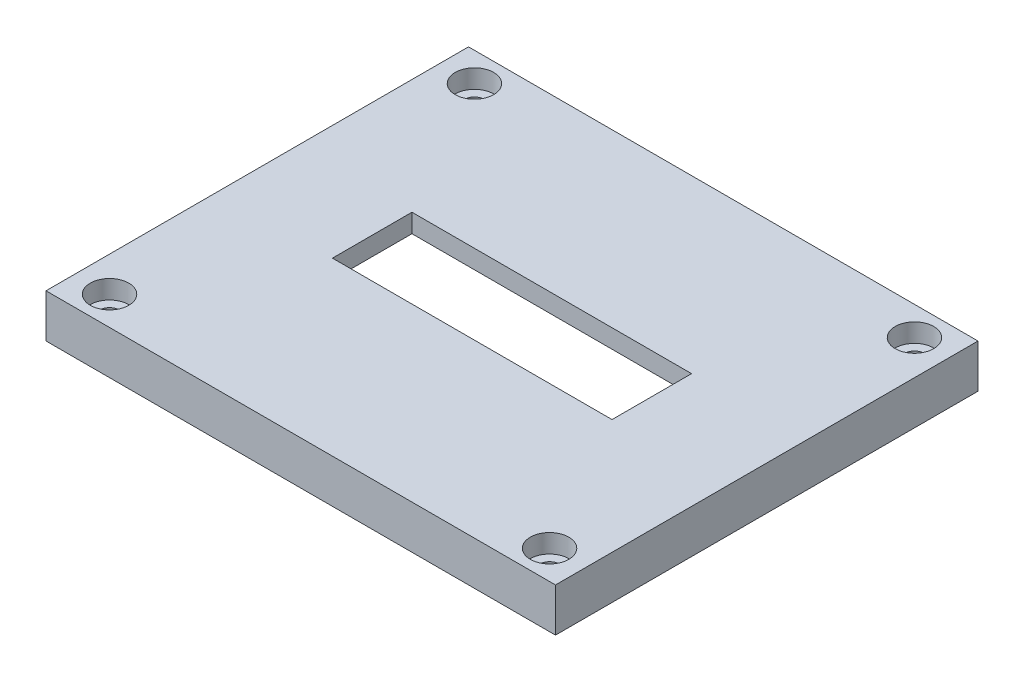
SolidWorks part; units mm, degrees
ref_plane "Спереди" through (0, 0, 0) normal (0, 0, 1) x (1, 0, 0)
ref_plane "Сверху" through (0, 0, 0) normal (0, 1, 0) x (1, 0, 0)
ref_plane "Справа" through (0, 0, 0) normal (1, 0, 0) x (0, 0, -1)
sketch "Sketch1" plane through (0, 0, 0) normal (0, 1, 0) x (1, 0, 0)
  line L1 (38, -31) -> (-38, -31)
  line L2 (38, -31) -> (38, 31)
  line L3 (38, 31) -> (-38, 31)
  line L4 (-38, -31) -> (-38, 31)
  line L5 (38, -31) -> (-38, 31) construction
  line L6 (38, 31) -> (-38, -31) construction
  point P0 (0, 0)
  dimension "D1" = 76
  dimension "D2" = 62
extrude "Boss-Extrude1" add sketch "Sketch1" along normal blind 2
sketch "Sketch2" plane through (0, 2, 0) normal (0, 1, 0) x (1, 0, 0)
  line L1 (-41, 34) -> (41, 34)
  line L2 (-41, 34) -> (-41, -34)
  line L3 (-41, -34) -> (41, -34)
  line L4 (41, 34) -> (41, -34)
  line L5 (-41, 34) -> (41, -34) construction
  line L6 (-41, -34) -> (41, 34) construction
  point P0 (0, 0)
  dimension "D1" = 82
  dimension "D2" = 68
extrude "Boss-Extrude2" add sketch "Sketch2" along normal blind 8
sketch "Sketch3" plane through (0, 0, 0) normal (0, -1, 0) x (1, 0, 0)
  line L0 (38, 0) -> (-38, 0) construction
  line L3 (38, 31) -> (38, -31) construction
  line L4 (-38, -31) -> (-38, 31) construction
  line L9 (-22.5, 6.4) -> (22.5, 6.4)
  line L10 (-22.5, 6.4) -> (-22.5, -6.4)
  line L11 (-22.5, -6.4) -> (22.5, -6.4)
  line L12 (22.5, 6.4) -> (22.5, -6.4)
  line L13 (-22.5, 6.4) -> (22.5, -6.4) construction
  line L14 (-22.5, -6.4) -> (22.5, 6.4) construction
  point P6 (0, 0)
  dimension "D1" = 45
  dimension "D2" = 12.8
extrude "Cut-Extrude1" cut sketch "Sketch3" against normal through all
sketch "Sketch4" plane through (0, 10, 0) normal (0, 1, 0) x (1, 0, 0)
  line L0 (41, 34) -> (-41, -34) construction
  line L1 (-41, 34) -> (41, -34) construction
  line L2 (-35.4089, 29.3635) -> (35.4089, 29.3635) construction
  line L3 (35.4089, 29.3635) -> (35.4089, -29.3635) construction
  line L4 (35.4089, -29.3635) -> (-35.4089, -29.3635) construction
  line L5 (-35.4089, -29.3635) -> (-35.4089, 29.3635) construction
  line L7 (-35.4089, -29.3635) -> (35.4089, 29.3635) construction
  line L8 (-35.4089, 29.3635) -> (35.4089, -29.3635) construction
  circle A0 centre (-35.4089, 29.3635) radius 1.6
  circle A1 centre (35.4089, 29.3635) radius 1.6
  circle A2 centre (35.4089, -29.3635) radius 1.6
  circle A3 centre (-35.4089, -29.3635) radius 1.6
  point P8 (0, 0)
  dimension "D2" = 3.2
  dimension "D1" = 92
extrude "Cut-Extrude2" cut sketch "Sketch4" against normal through all
sketch "Sketch5" plane through (0, 10, 0) normal (0, 1, 0) x (1, 0, 0)
  circle A0 centre (-35.4089, 29.3635) radius 3.1
  circle A1 centre (35.4089, 29.3635) radius 3.1
  circle A2 centre (35.4089, -29.3635) radius 3.1
  circle A3 centre (-35.4089, -29.3635) radius 3.1
  dimension "D1" = 6.2
extrude "Cut-Extrude3" cut sketch "Sketch5" against normal blind 3
sketch "Sketch9" plane through (0, 0, 0) normal (0, -1, 0) x (1, 0, 0)
  line L0 (-38, 31) -> (38, 31) construction
  line L1 (37.8, -30.8) -> (-37.8, -30.8)
  line L2 (37.8, -30.8) -> (37.8, 30.8)
  line L3 (37.8, 30.8) -> (-37.8, 30.8)
  line L4 (-37.8, -30.8) -> (-37.8, 30.8)
  line L5 (37.8, -30.8) -> (-37.8, 30.8) construction
  line L6 (37.8, 30.8) -> (-37.8, -30.8) construction
  line L7 (-38, -31) -> (-38, 31) construction
  point P0 (0, 0)
  dimension "D1" = 0.2
  dimension "D2" = 0.2
extrude "Cut-Extrude5" cut sketch "Sketch9" against normal blind 3 flip side to cut
sketch "Sketch10" plane through (0, 0, 0) normal (0, -1, 0) x (1, 0, 0)
  line L0 (-37.8, -30.8) -> (-31.8, -30.8)
  line L1 (-37.8, 24.8) -> (-37.8, 30.8)
  line L2 (34.7044, -30.8) -> (-34.7044, -30.8) construction
  line L3 (-37.8, 30.8) -> (-31.8, 30.8)
  line L4 (-31.8, -30.8) -> (-37.8, -24.8)
  line L5 (-37.8, 30.8) -> (-37.8, -30.8) construction
  line L6 (-37.8, -24.8) -> (-37.8, -30.8)
  line L7 (-34.7044, 30.8) -> (34.7044, 30.8) construction
  line L8 (-31.8, 30.8) -> (-37.8, 24.8)
  line L9 (37.8, 30.8) -> (37.8, 24.8)
  line L10 (37.8, -30.8) -> (37.8, 30.8) construction
  line L11 (37.8, 24.8) -> (31.8, 30.8)
  line L12 (31.8, 30.8) -> (37.8, 30.8)
  line L13 (37.8, -30.8) -> (31.8, -30.8)
  line L14 (31.8, -30.8) -> (37.8, -24.8)
  line L15 (37.8, -24.8) -> (37.8, -30.8)
  dimension "D1" = 6
extrude "Cut-Extrude6" cut sketch "Sketch10" against normal blind 3
sketch "Sketch11" plane through (0, 0, 0) normal (0, -1, 0) x (1, 0, 0)
  line L1 (-33, -27) -> (33, -27)
  line L2 (-33, -27) -> (-33, 27)
  line L3 (-33, 27) -> (33, 27)
  line L4 (33, -27) -> (33, 27)
  line L5 (-33, -27) -> (33, 27) construction
  line L6 (-33, 27) -> (33, -27) construction
  point P0 (0, 0)
  dimension "D1" = 54
  dimension "D2" = 66
extrude "Cut-Extrude7" cut sketch "Sketch11" against normal blind 7
chamfer "Chamfer2" distance 2 angle 10 2 edges at (-37.8, 0, 0) (37.8, 0, 0)
chamfer "Chamfer3" distance 1 angle 60 2 edges at (0, 0, 30.8) (0, 0, -30.8)
